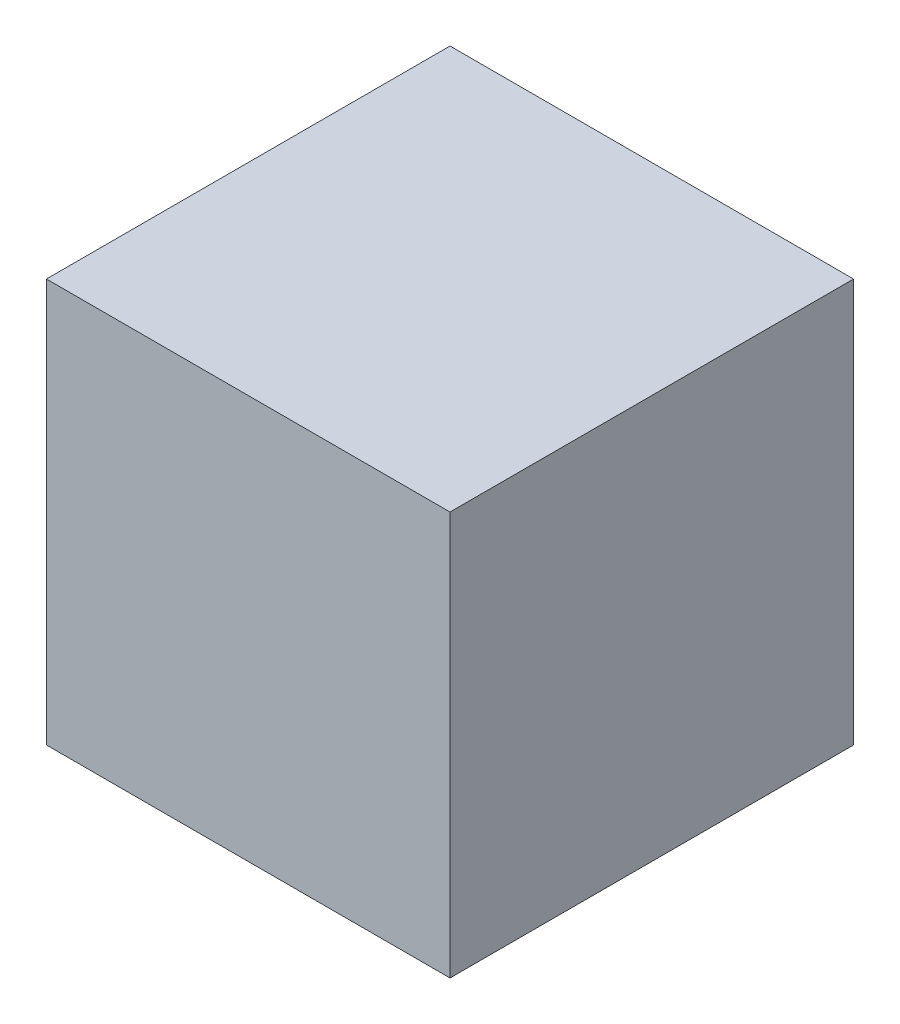
SolidWorks part; units mm, degrees
ref_plane "Front Plane" through (0, 0, 0) normal (0, 0, 1) x (1, 0, 0)
ref_plane "Top Plane" through (0, 0, 0) normal (0, 1, 0) x (1, 0, 0)
ref_plane "Right Plane" through (0, 0, 0) normal (1, 0, 0) x (0, 0, -1)
sketch "Sketch1" plane through (0, 0, 0) normal (0, 1, 0) x (1, 0, 0)
  line L1 (76.2, -76.2) -> (-76.2, -76.2)
  line L2 (76.2, -76.2) -> (76.2, 76.2)
  line L3 (76.2, 76.2) -> (-76.2, 76.2)
  line L4 (-76.2, -76.2) -> (-76.2, 76.2)
  line L5 (76.2, -76.2) -> (-76.2, 76.2) construction
  line L6 (76.2, 76.2) -> (-76.2, -76.2) construction
  point P0 (0, 0)
  dimension "D1" = 152.4
extrude "Boss-Extrude1" add sketch "Sketch1" along normal blind 152.4
